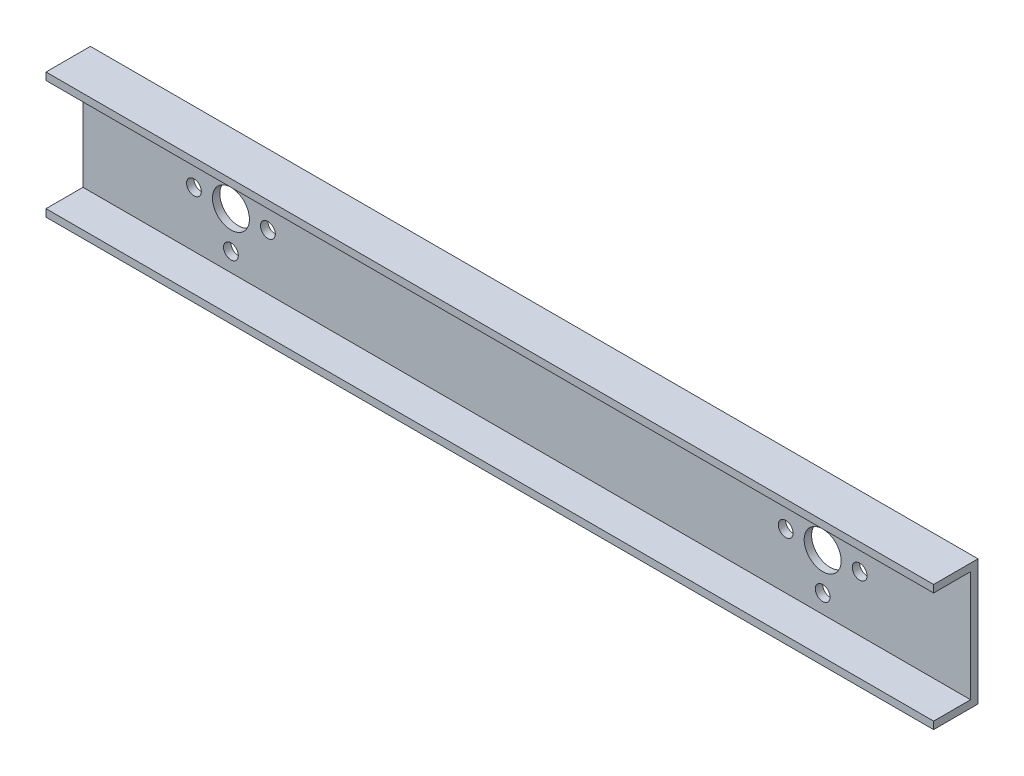
SolidWorks part; units mm, degrees
ref_plane "Front Plane" through (0, 0, 0) normal (0, 0, 1) x (1, 0, 0)
ref_plane "Top Plane" through (0, 0, 0) normal (0, 1, 0) x (1, 0, 0)
ref_plane "Right Plane" through (0, 0, 0) normal (1, 0, 0) x (0, 0, -1)
sketch "Sketch1" plane through (0, 0, 0) normal (1, 0, 0) x (0, 0, -1)
  line L0 (-25, 75) -> (-25, 85)
  line L1 (-25, 75) -> (25, 75)
  line L3 (-25, -75) -> (25, -75)
  line L4 (25, 75) -> (25, -75)
  line L5 (0, -75) -> (0, 75) construction
  line L6 (-25, 0) -> (25, 0) construction
  line L7 (-25, 85) -> (35, 85)
  line L8 (35, 85) -> (35, -85)
  line L9 (35, -85) -> (-25, -85)
  line L10 (-25, -85) -> (-25, -75)
  point P0 (0, 0)
extrude "Boss-Extrude2" add sketch "Sketch1" along normal blind 1200
sketch "Sketch2" plane through (0, 0, -25) normal (0, 0, 1) x (1, 0, 0)
  line L0 (1000, 0) -> (1200, 0) construction
  line L1 (1200, 75) -> (1200, -75) construction
  circle A0 centre (1000, 0) radius 25
  circle A1 centre (1000, 0) radius 50 construction
  circle A2 centre (950, 0) radius 10
  circle A3 centre (1000, 50) radius 10
  circle A4 centre (1000, -50) radius 10
  circle A5 centre (1050, 0) radius 10
extrude "Cut-Extrude1" cut sketch "Sketch2" against normal blind 1200
ref_plane "Plane1" through (600, 0, 0) normal (1, 0, 0) x (0, 0, -1)
mirror "Mirror2" about plane through (600, 0, 0) normal (1, 0, 0) of "Cut-Extrude1"
